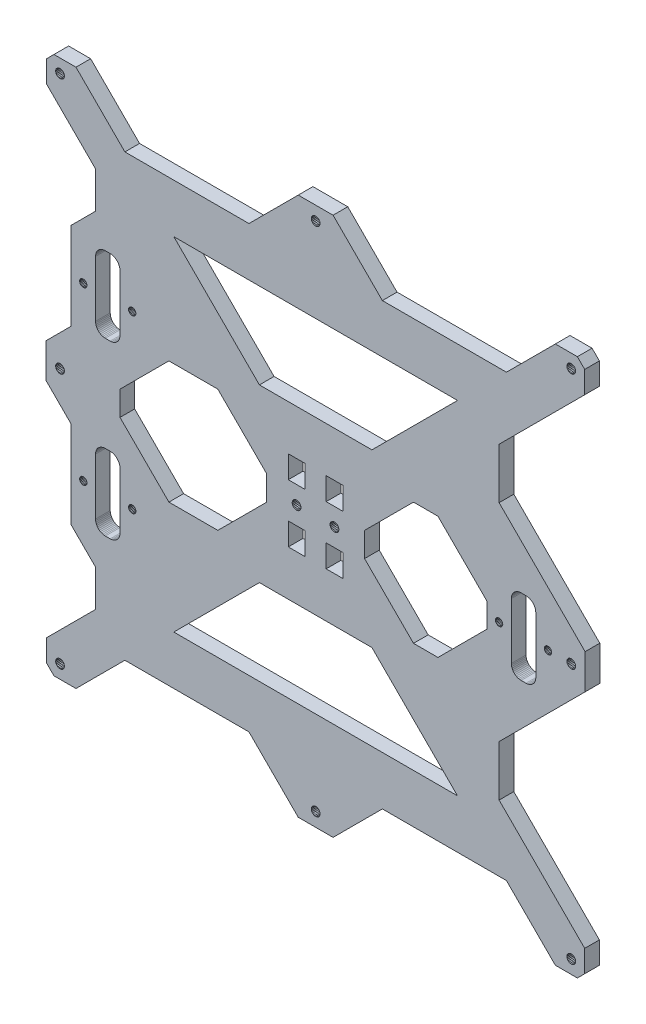
SolidWorks part; units mm, degrees
material "Maple"
ref_plane "Front Plane" through (0, 0, 0) normal (0, 0, 1) x (1, 0, 0)
ref_plane "Top Plane" through (0, 0, 0) normal (0, 1, 0) x (1, 0, 0)
ref_plane "Right Plane" through (0, 0, 0) normal (1, 0, 0) x (0, 0, -1)
sketch "Sketch1" plane through (0, 0, 0) normal (0, 0, 1) x (1, 0, 0)
  line L6332 (263.5741, 229.7904) -> (263.1048, 229.5589)
  line L6333 (262.6698, 229.2683) -> (262.2764, 228.9233)
  line L6334 (263.1048, 229.5589) -> (262.6698, 229.2683)
  line L6335 (253.1049, 139.0949) -> (273.1048, 159.0949)
  line L6336 (251.1049, 196.0949) -> (261.1048, 186.0949)
  line L6337 (261.1048, 312.0948) -> (251.1049, 302.0948)
  line L6338 (241.1049, 151.0949) -> (241.1049, 142.0949)
  line L6339 (274.8058, 284.8448) -> (274.656, 284.4831)
  line L6340 (269.9333, 200.2664) -> (270.2783, 200.6598)
  line L6341 (268.6356, 229.7904) -> (268.1401, 229.9585)
  line L6342 (268.1401, 229.9585) -> (267.627, 230.0606)
  line L6343 (267.627, 230.0606) -> (267.1048, 230.0948)
  line L6344 (241.1049, 142.0949) -> (244.1049, 139.0949)
  line L6345 (271.0706, 202.5727) -> (271.1048, 203.0948)
  line L6346 (267.627, 199.1291) -> (268.1401, 199.2311)
  line L6347 (263.5741, 199.3993) -> (264.0696, 199.2311)
  line L6348 (263.1048, 199.6307) -> (263.5741, 199.3993)
  line L6349 (461.1048, 347.0948) -> (426.1048, 312.0948)
  line L6350 (269.1048, 229.5589) -> (268.6356, 229.7904)
  line L6351 (261.4093, 227.6256) -> (261.2411, 227.1301)
  line L6352 (261.2411, 227.1301) -> (261.1391, 226.6169)
  line L6353 (261.1391, 226.6169) -> (261.1048, 226.0948)
  line L6354 (265.1048, 230.0948) -> (267.1048, 230.0948)
  line L6355 (449.1048, 139.0949) -> (429.1048, 159.0949)
  line L6356 (253.1049, 359.0948) -> (273.1048, 339.0948)
  line L6357 (262.6698, 199.9214) -> (263.1048, 199.6307)
  line L6358 (262.2764, 200.2664) -> (262.6698, 199.9214)
  line L6359 (267.1048, 199.0949) -> (265.1048, 199.0949)
  line L6360 (265.1048, 230.0948) -> (264.5827, 230.0606)
  line L6361 (264.5827, 230.0606) -> (264.0696, 229.9585)
  line L6362 (261.1048, 203.0948) -> (261.1048, 226.0948)
  line L6363 (261.1048, 203.0948) -> (261.1391, 202.5727)
  line L6364 (261.1391, 202.5727) -> (261.2411, 202.0596)
  line L6365 (241.1049, 347.0948) -> (261.1048, 327.0948)
  line L6366 (270.9686, 227.1301) -> (270.8004, 227.6256)
  line L6367 (271.0706, 226.6169) -> (270.9686, 227.1301)
  line L6368 (271.1048, 226.0948) -> (271.0706, 226.6169)
  line L6369 (244.1049, 359.0948) -> (241.1049, 356.0948)
  line L6370 (458.1048, 359.0948) -> (449.1048, 359.0948)
  line L6371 (251.1049, 231.7916) -> (251.1049, 196.0949)
  line L6372 (270.8004, 227.6256) -> (270.5689, 228.0948)
  line L6373 (270.5689, 228.0948) -> (270.2783, 228.5299)
  line L6374 (461.1048, 151.0949) -> (461.1048, 142.0949)
  line L6375 (261.1048, 171.0949) -> (261.1048, 186.0949)
  line L6376 (261.4093, 201.5641) -> (261.6407, 201.0949)
  line L6377 (261.6407, 201.0949) -> (261.9314, 200.6598)
  line L6378 (270.2783, 228.5299) -> (269.9333, 228.9233)
  line L6379 (261.9314, 200.6598) -> (262.2764, 200.2664)
  line L6380 (271.1048, 226.0948) -> (271.1048, 203.0948)
  line L6381 (261.6407, 228.0948) -> (261.4093, 227.6256)
  line L6382 (268.6356, 199.3993) -> (269.1048, 199.6307)
  line L6383 (269.1048, 199.6307) -> (269.5399, 199.9214)
  line L6384 (269.5399, 199.9214) -> (269.9333, 200.2664)
  line L6385 (268.1401, 199.2311) -> (268.6356, 199.3993)
  line L6386 (458.1048, 139.0949) -> (461.1048, 142.0949)
  line L6387 (270.8004, 201.5641) -> (270.9686, 202.0596)
  line L6388 (270.9686, 202.0596) -> (271.0706, 202.5727)
  line L6389 (269.5399, 229.2683) -> (269.1048, 229.5589)
  line L6390 (269.9333, 228.9233) -> (269.5399, 229.2683)
  line L6391 (449.1048, 359.0948) -> (429.1048, 339.0948)
  line L6392 (241.1049, 151.0949) -> (261.1048, 171.0949)
  line L6393 (261.1048, 327.0948) -> (261.1048, 312.0948)
  line L6394 (264.0696, 229.9585) -> (263.5741, 229.7904)
  line L6395 (461.1048, 356.0948) -> (458.1048, 359.0948)
  line L6396 (251.1049, 302.0948) -> (251.1049, 266.3687)
  line L6397 (267.1048, 199.0949) -> (267.627, 199.1291)
  line L6398 (264.0696, 199.2311) -> (264.5827, 199.1291)
  line L6399 (261.9314, 228.5299) -> (261.6407, 228.0948)
  line L6400 (262.2764, 228.9233) -> (261.9314, 228.5299)
  line L6401 (270.2783, 200.6598) -> (270.5689, 201.0949)
  line L6402 (270.5689, 201.0949) -> (270.8004, 201.5641)
  line L6403 (261.2411, 202.0596) -> (261.4093, 201.5641)
  line L6404 (264.5827, 199.1291) -> (265.1048, 199.0949)
  line L6405 (445.0441, 248.0342) -> (445.3548, 247.7958)
  line L6406 (427.4038, 249.8448) -> (427.1655, 250.1555)
  line L6407 (358.2261, 359.2474) -> (343.9835, 359.2474)
  line L6408 (343.9835, 138.9423) -> (358.2261, 138.9423)
  line L6409 (240.9376, 256.2015) -> (240.9376, 241.9588)
  line L6410 (273.1048, 339.0948) -> (323.831, 339.0948)
  line L6411 (378.3787, 339.0948) -> (429.1048, 339.0948)
  line L6412 (426.1048, 186.0949) -> (426.1048, 206.821)
  line L6413 (273.1048, 159.0949) -> (323.831, 159.0949)
  line L6414 (378.3787, 159.0949) -> (429.1048, 159.0949)
  line L6415 (461.272, 241.9882) -> (461.272, 256.2308)
  line L6416 (426.1048, 291.3981) -> (426.1048, 312.0948)
  line L6417 (433.5741, 263.6532) -> (433.1048, 263.4218)
  line L6418 (270.9686, 297.1371) -> (270.8004, 297.6326)
  line L6419 (270.8004, 297.6326) -> (270.5689, 298.1019)
  line L6420 (433.1048, 263.4218) -> (432.6697, 263.1311)
  line L6421 (270.2783, 298.5369) -> (269.9333, 298.9303)
  line L6422 (275.0442, 285.1555) -> (274.8058, 284.8448)
  line L6423 (275.3548, 285.3939) -> (275.0442, 285.1555)
  line L6424 (275.7166, 285.5437) -> (275.3548, 285.3939)
  line L6425 (276.1048, 285.5948) -> (275.7166, 285.5437)
  line L6426 (276.4931, 285.5437) -> (276.1048, 285.5948)
  line L6427 (276.8548, 285.3939) -> (276.4931, 285.5437)
  line L6428 (277.1655, 285.1555) -> (276.8548, 285.3939)
  line L6429 (277.4039, 284.8448) -> (277.1655, 285.1555)
  line L6430 (277.5537, 284.4831) -> (277.4039, 284.8448)
  line L6431 (277.6048, 284.0948) -> (277.5537, 284.4831)
  line L6432 (277.5537, 283.7066) -> (277.6048, 284.0948)
  line L6433 (277.4039, 283.3448) -> (277.5537, 283.7066)
  line L6434 (277.1655, 283.0342) -> (277.4039, 283.3448)
  line L6435 (276.8548, 282.7958) -> (277.1655, 283.0342)
  line L6436 (276.4931, 282.6459) -> (276.8548, 282.7958)
  line L6437 (276.1048, 282.5948) -> (276.4931, 282.6459)
  line L6438 (275.7166, 282.6459) -> (276.1048, 282.5948)
  line L6439 (275.3548, 282.7958) -> (275.7166, 282.6459)
  line L6440 (275.0442, 283.0342) -> (275.3548, 282.7958)
  line L6441 (274.8058, 283.3448) -> (275.0442, 283.0342)
  line L6442 (274.656, 283.7066) -> (274.8058, 283.3448)
  line L6443 (274.6048, 284.0948) -> (274.656, 283.7066)
  line L6444 (274.656, 284.4831) -> (274.6048, 284.0948)
  line L6445 (444.8058, 248.3448) -> (445.0441, 248.0342)
  line L6446 (444.6559, 248.7066) -> (444.8058, 248.3448)
  line L6447 (444.6048, 249.0948) -> (444.6559, 248.7066)
  line L6448 (444.6559, 249.4831) -> (444.6048, 249.0948)
  line L6449 (444.8058, 249.8448) -> (444.6559, 249.4831)
  line L6450 (445.0441, 250.1555) -> (444.8058, 249.8448)
  line L6451 (445.3548, 250.3939) -> (445.0441, 250.1555)
  line L6452 (445.7166, 250.5437) -> (445.3548, 250.3939)
  line L6453 (446.1048, 250.5948) -> (445.7166, 250.5437)
  line L6454 (446.493, 250.5437) -> (446.1048, 250.5948)
  line L6455 (446.8548, 250.3939) -> (446.493, 250.5437)
  line L6456 (447.1655, 250.1555) -> (446.8548, 250.3939)
  line L6457 (447.4038, 249.8448) -> (447.1655, 250.1555)
  line L6458 (447.6048, 249.0948) -> (447.5537, 249.4831)
  line L6459 (447.5537, 248.7066) -> (447.6048, 249.0948)
  line L6460 (447.1655, 248.0342) -> (447.4038, 248.3448)
  line L6461 (446.8548, 247.7958) -> (447.1655, 248.0342)
  line L6462 (446.493, 247.6459) -> (446.8548, 247.7958)
  line L6463 (446.1048, 247.5948) -> (446.493, 247.6459)
  line L6464 (445.7166, 247.6459) -> (446.1048, 247.5948)
  line L6465 (445.3548, 247.7958) -> (445.7166, 247.6459)
  line L6466 (427.5537, 249.4831) -> (427.4038, 249.8448)
  line L6467 (427.6048, 249.0948) -> (427.5537, 249.4831)
  line L6468 (427.5537, 248.7066) -> (427.6048, 249.0948)
  line L6469 (427.4038, 248.3448) -> (427.5537, 248.7066)
  line L6470 (427.1655, 248.0342) -> (427.4038, 248.3448)
  line L6471 (426.8548, 247.7958) -> (427.1655, 248.0342)
  line L6472 (426.493, 247.6459) -> (426.8548, 247.7958)
  line L6473 (426.1048, 247.5948) -> (426.493, 247.6459)
  line L6474 (425.7166, 247.6459) -> (426.1048, 247.5948)
  line L6475 (425.3548, 247.7958) -> (425.7166, 247.6459)
  line L6476 (425.0441, 248.0342) -> (425.3548, 247.7958)
  line L6477 (424.8058, 248.3448) -> (425.0441, 248.0342)
  line L6478 (424.6559, 248.7066) -> (424.8058, 248.3448)
  line L6479 (424.6048, 249.0948) -> (424.6559, 248.7066)
  line L6480 (424.6559, 249.4831) -> (424.6048, 249.0948)
  line L6481 (424.8058, 249.8448) -> (424.6559, 249.4831)
  line L6482 (425.0441, 250.1555) -> (424.8058, 249.8448)
  line L6483 (425.3548, 250.3939) -> (425.0441, 250.1555)
  line L6484 (425.7166, 250.5437) -> (425.3548, 250.3939)
  line L6485 (426.1048, 250.5948) -> (425.7166, 250.5437)
  line L6486 (426.493, 250.5437) -> (426.1048, 250.5948)
  line L6487 (426.8548, 250.3939) -> (426.493, 250.5437)
  line L6488 (427.1655, 250.1555) -> (426.8548, 250.3939)
  line L6489 (434.0695, 263.8214) -> (433.5741, 263.6532)
  line L6490 (434.5827, 263.9235) -> (434.0695, 263.8214)
  line L6491 (435.1048, 263.9577) -> (434.5827, 263.9235)
  line L6492 (435.1048, 263.9577) -> (437.1048, 263.9577)
  line L6493 (437.6269, 263.9235) -> (437.1048, 263.9577)
  line L6494 (438.1401, 263.8214) -> (437.6269, 263.9235)
  line L6495 (438.6355, 263.6532) -> (438.1401, 263.8214)
  line L6496 (439.1048, 263.4218) -> (438.6355, 263.6532)
  line L6497 (439.5398, 263.1311) -> (439.1048, 263.4218)
  line L6498 (439.9332, 262.7861) -> (439.5398, 263.1311)
  line L6499 (440.2782, 262.3928) -> (439.9332, 262.7861)
  line L6500 (440.5689, 261.9577) -> (440.2782, 262.3928)
  line L6501 (440.8003, 261.4884) -> (440.5689, 261.9577)
  line L6502 (440.9685, 260.993) -> (440.8003, 261.4884)
  line L6503 (441.0706, 260.4798) -> (440.9685, 260.993)
  line L6504 (441.1048, 259.9577) -> (441.0706, 260.4798)
  line L6505 (441.1048, 259.9577) -> (441.1048, 236.9577)
  line L6506 (441.0706, 236.4356) -> (441.1048, 236.9577)
  line L6507 (440.9685, 235.9224) -> (441.0706, 236.4356)
  line L6508 (440.8003, 235.427) -> (440.9685, 235.9224)
  line L6509 (440.5689, 234.9577) -> (440.8003, 235.427)
  line L6510 (440.2782, 234.5227) -> (440.5689, 234.9577)
  line L6511 (439.9332, 234.1293) -> (440.2782, 234.5227)
  line L6512 (439.5398, 233.7843) -> (439.9332, 234.1293)
  line L6513 (439.1048, 233.4936) -> (439.5398, 233.7843)
  line L6514 (438.6355, 233.2622) -> (439.1048, 233.4936)
  line L6515 (438.1401, 233.094) -> (438.6355, 233.2622)
  line L6516 (437.6269, 232.9919) -> (438.1401, 233.094)
  line L6517 (437.1048, 232.9577) -> (437.6269, 232.9919)
  line L6518 (437.1048, 232.9577) -> (435.1048, 232.9577)
  line L6519 (434.5827, 232.9919) -> (435.1048, 232.9577)
  line L6520 (434.0695, 233.094) -> (434.5827, 232.9919)
  line L6521 (433.5741, 233.2622) -> (434.0695, 233.094)
  line L6522 (433.1048, 233.4936) -> (433.5741, 233.2622)
  line L6523 (432.6697, 233.7843) -> (433.1048, 233.4936)
  line L6524 (432.2764, 234.1293) -> (432.6697, 233.7843)
  line L6525 (431.9314, 234.5227) -> (432.2764, 234.1293)
  line L6526 (431.6407, 234.9577) -> (431.9314, 234.5227)
  line L6527 (431.4093, 235.427) -> (431.6407, 234.9577)
  line L6528 (431.2411, 235.9224) -> (431.4093, 235.427)
  line L6529 (431.139, 236.4356) -> (431.2411, 235.9224)
  line L6530 (431.1048, 236.9577) -> (431.139, 236.4356)
  line L6531 (431.1048, 236.9577) -> (431.1048, 259.9577)
  line L6532 (431.139, 260.4798) -> (431.1048, 259.9577)
  line L6533 (431.2411, 260.993) -> (431.139, 260.4798)
  line L6534 (431.4093, 261.4884) -> (431.2411, 260.993)
  line L6535 (431.6407, 261.9577) -> (431.4093, 261.4884)
  line L6536 (431.9314, 262.3928) -> (431.6407, 261.9577)
  line L6537 (432.2764, 262.7861) -> (431.9314, 262.3928)
  line L6538 (432.6697, 263.1311) -> (432.2764, 262.7861)
  line L6539 (271.0706, 296.624) -> (270.9686, 297.1371)
  line L6540 (271.1048, 296.1019) -> (271.0706, 296.624)
  line L6541 (271.1048, 296.1019) -> (271.1048, 273.1019)
  line L6542 (271.0706, 272.5798) -> (271.1048, 273.1019)
  line L6543 (270.9686, 272.0666) -> (271.0706, 272.5798)
  line L6544 (270.8004, 271.5711) -> (270.9686, 272.0666)
  line L6545 (270.5689, 271.1019) -> (270.8004, 271.5711)
  line L6546 (270.2783, 270.6668) -> (270.5689, 271.1019)
  line L6547 (269.9333, 270.2734) -> (270.2783, 270.6668)
  line L6548 (269.5399, 269.9285) -> (269.9333, 270.2734)
  line L6549 (269.1048, 269.6378) -> (269.5399, 269.9285)
  line L6550 (268.6356, 269.4063) -> (269.1048, 269.6378)
  line L6551 (268.1401, 269.2382) -> (268.6356, 269.4063)
  line L6552 (267.627, 269.1361) -> (268.1401, 269.2382)
  line L6553 (267.1048, 269.1019) -> (267.627, 269.1361)
  line L6554 (267.1048, 269.1019) -> (265.1048, 269.1019)
  line L6555 (264.5827, 269.1361) -> (265.1048, 269.1019)
  line L6556 (264.0696, 269.2382) -> (264.5827, 269.1361)
  line L6557 (263.5741, 269.4063) -> (264.0696, 269.2382)
  line L6558 (263.1048, 269.6378) -> (263.5741, 269.4063)
  line L6559 (262.6698, 269.9285) -> (263.1048, 269.6378)
  line L6560 (262.2764, 270.2734) -> (262.6698, 269.9285)
  line L6561 (261.9314, 270.6668) -> (262.2764, 270.2734)
  line L6562 (261.6407, 271.1019) -> (261.9314, 270.6668)
  line L6563 (261.4093, 271.5711) -> (261.6407, 271.1019)
  line L6564 (261.2411, 272.0666) -> (261.4093, 271.5711)
  line L6565 (261.1391, 272.5798) -> (261.2411, 272.0666)
  line L6566 (261.1048, 273.1019) -> (261.1391, 272.5798)
  line L6567 (261.1048, 273.1019) -> (261.1048, 296.1019)
  line L6568 (261.1391, 296.624) -> (261.1048, 296.1019)
  line L6569 (261.2411, 297.1371) -> (261.1391, 296.624)
  line L6570 (261.4093, 297.6326) -> (261.2411, 297.1371)
  line L6571 (261.6407, 298.1019) -> (261.4093, 297.6326)
  line L6572 (261.9314, 298.5369) -> (261.6407, 298.1019)
  line L6573 (262.2764, 298.9303) -> (261.9314, 298.5369)
  line L6574 (262.6698, 299.2753) -> (262.2764, 298.9303)
  line L6575 (263.1048, 299.566) -> (262.6698, 299.2753)
  line L6576 (263.5741, 299.7974) -> (263.1048, 299.566)
  line L6577 (264.0696, 299.9656) -> (263.5741, 299.7974)
  line L6578 (264.5827, 300.0676) -> (264.0696, 299.9656)
  line L6579 (265.1048, 300.1019) -> (264.5827, 300.0676)
  line L6580 (265.1048, 300.1019) -> (267.1048, 300.1019)
  line L6581 (267.627, 300.0676) -> (267.1048, 300.1019)
  line L6582 (268.1401, 299.9656) -> (267.627, 300.0676)
  line L6583 (268.6356, 299.7974) -> (268.1401, 299.9656)
  line L6584 (269.1048, 299.566) -> (268.6356, 299.7974)
  line L6585 (269.5399, 299.2753) -> (269.1048, 299.566)
  line L6586 (269.9333, 298.9303) -> (269.5399, 299.2753)
  line L6587 (270.5689, 298.1019) -> (270.2783, 298.5369)
  line L6588 (276.8548, 212.7958) -> (277.1655, 213.0342)
  line L6589 (276.4931, 212.646) -> (276.8548, 212.7958)
  line L6590 (276.1048, 212.5948) -> (276.4931, 212.646)
  line L6591 (275.7166, 212.646) -> (276.1048, 212.5948)
  line L6592 (275.3548, 212.7958) -> (275.7166, 212.646)
  line L6593 (275.0442, 213.0342) -> (275.3548, 212.7958)
  line L6594 (274.8058, 213.3448) -> (275.0442, 213.0342)
  line L6595 (274.656, 213.7066) -> (274.8058, 213.3448)
  line L6596 (274.6048, 214.0948) -> (274.656, 213.7066)
  line L6597 (274.656, 214.4831) -> (274.6048, 214.0948)
  line L6598 (274.8058, 214.8448) -> (274.656, 214.4831)
  line L6599 (275.0442, 215.1555) -> (274.8058, 214.8448)
  line L6600 (275.3548, 215.3939) -> (275.0442, 215.1555)
  line L6601 (275.7166, 215.5437) -> (275.3548, 215.3939)
  line L6602 (276.1048, 215.5948) -> (275.7166, 215.5437)
  line L6603 (276.4931, 215.5437) -> (276.1048, 215.5948)
  line L6604 (276.8548, 215.3939) -> (276.4931, 215.5437)
  line L6605 (277.1655, 215.1555) -> (276.8548, 215.3939)
  line L6606 (277.4039, 214.8448) -> (277.1655, 215.1555)
  line L6607 (277.5537, 214.4831) -> (277.4039, 214.8448)
  line L6608 (277.6048, 214.0948) -> (277.5537, 214.4831)
  line L6609 (277.5537, 213.7066) -> (277.6048, 214.0948)
  line L6610 (277.4039, 213.3448) -> (277.5537, 213.7066)
  line L6611 (277.1655, 213.0342) -> (277.4039, 213.3448)
  line L6612 (352.6637, 352.7052) -> (352.8435, 353.1393)
  line L6613 (352.3776, 352.3324) -> (352.6637, 352.7052)
  line L6614 (352.0048, 352.0463) -> (352.3776, 352.3324)
  line L6615 (351.5707, 351.8665) -> (352.0048, 352.0463)
  line L6616 (351.1048, 351.8052) -> (351.5707, 351.8665)
  line L6617 (350.6389, 351.8665) -> (351.1048, 351.8052)
  line L6618 (350.2048, 352.0463) -> (350.6389, 351.8665)
  line L6619 (349.832, 352.3324) -> (350.2048, 352.0463)
  line L6620 (349.546, 352.7052) -> (349.832, 352.3324)
  line L6621 (349.3662, 353.1393) -> (349.546, 352.7052)
  line L6622 (349.3048, 353.6052) -> (349.3662, 353.1393)
  line L6623 (349.3662, 354.0711) -> (349.3048, 353.6052)
  line L6624 (349.546, 354.5052) -> (349.3662, 354.0711)
  line L6625 (349.832, 354.878) -> (349.546, 354.5052)
  line L6626 (350.2048, 355.164) -> (349.832, 354.878)
  line L6627 (351.1048, 355.4052) -> (350.6389, 355.3438)
  line L6628 (351.5707, 355.3438) -> (351.1048, 355.4052)
  line L6629 (352.0048, 355.164) -> (351.5707, 355.3438)
  line L6630 (352.0385, 355.1317) -> (352.0048, 355.164)
  line L6631 (352.3776, 354.878) -> (352.0385, 355.1317)
  line L6632 (352.6637, 354.5052) -> (352.3776, 354.878)
  line L6633 (352.8435, 354.0711) -> (352.6637, 354.5052)
  line L6634 (352.9048, 353.6052) -> (352.8435, 354.0711)
  line L6635 (352.8435, 353.1393) -> (352.9048, 353.6052)
  line L6636 (256.1049, 285.5948) -> (255.7166, 285.5437)
  line L6637 (256.4931, 285.5437) -> (256.1049, 285.5948)
  line L6638 (256.8549, 285.3939) -> (256.4931, 285.5437)
  line L6639 (257.1655, 285.1555) -> (256.8549, 285.3939)
  line L6640 (257.4039, 284.8448) -> (257.1655, 285.1555)
  line L6641 (257.5537, 284.4831) -> (257.4039, 284.8448)
  line L6642 (257.6049, 284.0948) -> (257.5537, 284.4831)
  line L6643 (257.5537, 283.7066) -> (257.6049, 284.0948)
  line L6644 (257.4039, 283.3448) -> (257.5537, 283.7066)
  line L6645 (257.1655, 283.0342) -> (257.4039, 283.3448)
  line L6646 (256.8549, 282.7958) -> (257.1655, 283.0342)
  line L6647 (256.4931, 282.6459) -> (256.8549, 282.7958)
  line L6648 (256.1049, 282.5948) -> (256.4931, 282.6459)
  line L6649 (255.7166, 282.6459) -> (256.1049, 282.5948)
  line L6650 (255.3549, 282.7958) -> (255.7166, 282.6459)
  line L6651 (255.0442, 283.0342) -> (255.3549, 282.7958)
  line L6652 (254.8058, 283.3448) -> (255.0442, 283.0342)
  line L6653 (254.656, 283.7066) -> (254.8058, 283.3448)
  line L6654 (254.6049, 284.0948) -> (254.656, 283.7066)
  line L6655 (254.656, 284.4831) -> (254.6049, 284.0948)
  line L6656 (254.8058, 284.8448) -> (254.656, 284.4831)
  line L6657 (255.0442, 285.1555) -> (254.8058, 284.8448)
  line L6658 (255.3549, 285.3939) -> (255.0442, 285.1555)
  line L6659 (255.7166, 285.5437) -> (255.3549, 285.3939)
  line L6660 (350.2048, 146.1433) -> (349.832, 145.8573)
  line L6661 (350.6389, 146.3232) -> (350.2048, 146.1433)
  line L6662 (351.1048, 146.3845) -> (350.6389, 146.3232)
  line L6663 (351.5707, 146.3232) -> (351.1048, 146.3845)
  line L6664 (352.0048, 146.1433) -> (351.5707, 146.3232)
  line L6665 (352.3776, 145.8573) -> (352.0048, 146.1433)
  line L6666 (352.6637, 145.4845) -> (352.3776, 145.8573)
  line L6667 (352.8435, 145.0504) -> (352.6637, 145.4845)
  line L6668 (352.9048, 144.5845) -> (352.8435, 145.0504)
  line L6669 (352.8435, 144.1186) -> (352.9048, 144.5845)
  line L6670 (352.6637, 143.6845) -> (352.8435, 144.1186)
  line L6671 (352.3776, 143.3117) -> (352.6637, 143.6845)
  line L6672 (352.0048, 143.0256) -> (352.3776, 143.3117)
  line L6673 (351.1048, 142.7845) -> (351.5707, 142.8458)
  line L6674 (350.6389, 142.8458) -> (351.1048, 142.7845)
  line L6675 (350.2048, 143.0256) -> (350.6389, 142.8458)
  line L6676 (350.1712, 143.0579) -> (350.2048, 143.0256)
  line L6677 (349.832, 143.3117) -> (350.1712, 143.0579)
  line L6678 (349.546, 143.6845) -> (349.832, 143.3117)
  line L6679 (349.3662, 144.1186) -> (349.546, 143.6845)
  line L6680 (349.3048, 144.5845) -> (349.3662, 144.1186)
  line L6681 (349.3662, 145.0504) -> (349.3048, 144.5845)
  line L6682 (349.546, 145.4845) -> (349.3662, 145.0504)
  line L6683 (349.832, 145.8573) -> (349.546, 145.4845)
  line L6684 (293.1048, 319.0948) -> (409.1048, 319.0948)
  line L6685 (409.1048, 319.0948) -> (374.1048, 284.0948)
  line L6686 (374.1048, 284.0948) -> (328.1048, 284.0948)
  line L6687 (293.1048, 319.0948) -> (328.1048, 284.0948)
  line L6688 (456.5152, 146.1433) -> (456.081, 146.3232)
  line L6689 (456.888, 145.8573) -> (456.5152, 146.1433)
  line L6690 (457.174, 145.4845) -> (456.888, 145.8573)
  line L6691 (457.3538, 145.0504) -> (457.174, 145.4845)
  line L6692 (457.4152, 144.5845) -> (457.3538, 145.0504)
  line L6693 (457.3538, 144.1186) -> (457.4152, 144.5845)
  line L6694 (457.174, 143.6845) -> (457.3538, 144.1186)
  line L6695 (456.888, 143.3117) -> (457.174, 143.6845)
  line L6696 (456.5152, 143.0256) -> (456.888, 143.3117)
  line L6697 (456.081, 142.8458) -> (456.5152, 143.0256)
  line L6698 (455.6152, 142.7845) -> (456.081, 142.8458)
  line L6699 (455.1493, 142.8458) -> (455.6152, 142.7845)
  line L6700 (454.7152, 143.0256) -> (455.1493, 142.8458)
  line L6701 (454.3424, 143.3117) -> (454.7152, 143.0256)
  line L6702 (454.0563, 143.6845) -> (454.3424, 143.3117)
  line L6703 (453.8765, 144.1186) -> (454.0563, 143.6845)
  line L6704 (453.8152, 144.5845) -> (453.8765, 144.1186)
  line L6705 (453.8765, 145.0504) -> (453.8152, 144.5845)
  line L6706 (454.0563, 145.4845) -> (453.8765, 145.0504)
  line L6707 (454.3424, 145.8573) -> (454.0563, 145.4845)
  line L6708 (454.7152, 146.1433) -> (454.3424, 145.8573)
  line L6709 (455.1493, 146.3232) -> (454.7152, 146.1433)
  line L6710 (455.6152, 146.3845) -> (455.1493, 146.3232)
  line L6711 (456.081, 146.3232) -> (455.6152, 146.3845)
  line L6712 (245.6771, 143.0566) -> (246.1092, 142.8719)
  line L6713 (245.3075, 143.3468) -> (245.6771, 143.0566)
  line L6714 (245.0257, 143.7227) -> (245.3075, 143.3468)
  line L6715 (244.8507, 144.1588) -> (245.0257, 143.7227)
  line L6716 (244.7946, 144.6254) -> (244.8507, 144.1588)
  line L6717 (244.8611, 145.0905) -> (244.7946, 144.6254)
  line L6718 (245.0458, 145.5226) -> (244.8611, 145.0905)
  line L6719 (245.336, 145.8922) -> (245.0458, 145.5226)
  line L6720 (245.712, 146.1741) -> (245.336, 145.8922)
  line L6721 (246.1481, 146.349) -> (245.712, 146.1741)
  line L6722 (246.6146, 146.4051) -> (246.1481, 146.349)
  line L6723 (247.0798, 146.3386) -> (246.6146, 146.4051)
  line L6724 (247.5118, 146.1539) -> (247.0798, 146.3386)
  line L6725 (247.8814, 145.8637) -> (247.5118, 146.1539)
  line L6726 (248.1633, 145.4878) -> (247.8814, 145.8637)
  line L6727 (248.3382, 145.0517) -> (248.1633, 145.4878)
  line L6728 (248.3944, 144.5851) -> (248.3382, 145.0517)
  line L6729 (248.3278, 144.12) -> (248.3944, 144.5851)
  line L6730 (248.1432, 143.6879) -> (248.3278, 144.12)
  line L6731 (247.853, 143.3183) -> (248.1432, 143.6879)
  line L6732 (247.477, 143.0364) -> (247.853, 143.3183)
  line L6733 (247.0409, 142.8615) -> (247.477, 143.0364)
  line L6734 (246.5743, 142.8054) -> (247.0409, 142.8615)
  line L6735 (246.1092, 142.8719) -> (246.5743, 142.8054)
  line L6736 (454.3567, 250.3818) -> (454.0665, 250.0122)
  line L6737 (454.7327, 250.6636) -> (454.3567, 250.3818)
  line L6738 (455.1688, 250.8386) -> (454.7327, 250.6636)
  line L6739 (455.6353, 250.8947) -> (455.1688, 250.8386)
  line L6740 (456.1005, 250.8282) -> (455.6353, 250.8947)
  line L6741 (456.5325, 250.6435) -> (456.1005, 250.8282)
  line L6742 (456.9021, 250.3533) -> (456.5325, 250.6435)
  line L6743 (457.184, 249.9773) -> (456.9021, 250.3533)
  line L6744 (457.3589, 249.5412) -> (457.184, 249.9773)
  line L6745 (457.4151, 249.0747) -> (457.3589, 249.5412)
  line L6746 (457.3485, 248.6095) -> (457.4151, 249.0747)
  line L6747 (457.1639, 248.1775) -> (457.3485, 248.6095)
  line L6748 (456.8736, 247.8079) -> (457.1639, 248.1775)
  line L6749 (456.4977, 247.526) -> (456.8736, 247.8079)
  line L6750 (456.0616, 247.3511) -> (456.4977, 247.526)
  line L6751 (455.595, 247.2949) -> (456.0616, 247.3511)
  line L6752 (455.1299, 247.3615) -> (455.595, 247.2949)
  line L6753 (454.6978, 247.5462) -> (455.1299, 247.3615)
  line L6754 (454.3282, 247.8364) -> (454.6978, 247.5462)
  line L6755 (454.0464, 248.2123) -> (454.3282, 247.8364)
  line L6756 (453.8714, 248.6484) -> (454.0464, 248.2123)
  line L6757 (453.8153, 249.115) -> (453.8714, 248.6484)
  line L6758 (453.8818, 249.5801) -> (453.8153, 249.115)
  line L6759 (454.0665, 250.0122) -> (453.8818, 249.5801)
  line L6760 (244.7946, 249.115) -> (244.8507, 248.6484)
  line L6761 (244.8611, 249.5801) -> (244.7946, 249.115)
  line L6762 (245.0458, 250.0122) -> (244.8611, 249.5801)
  line L6763 (245.336, 250.3818) -> (245.0458, 250.0122)
  line L6764 (245.712, 250.6636) -> (245.336, 250.3818)
  line L6765 (246.1481, 250.8386) -> (245.712, 250.6636)
  line L6766 (246.6146, 250.8947) -> (246.1481, 250.8386)
  line L6767 (247.0798, 250.8282) -> (246.6146, 250.8947)
  line L6768 (247.5118, 250.6435) -> (247.0798, 250.8282)
  line L6769 (247.8814, 250.3533) -> (247.5118, 250.6435)
  line L6770 (248.1633, 249.9773) -> (247.8814, 250.3533)
  line L6771 (248.3382, 249.5412) -> (248.1633, 249.9773)
  line L6772 (248.3944, 249.0747) -> (248.3382, 249.5412)
  line L6773 (248.3278, 248.6095) -> (248.3944, 249.0747)
  line L6774 (248.1432, 248.1775) -> (248.3278, 248.6095)
  line L6775 (247.853, 247.8079) -> (248.1432, 248.1775)
  line L6776 (247.477, 247.526) -> (247.853, 247.8079)
  line L6777 (247.0409, 247.3511) -> (247.477, 247.526)
  line L6778 (246.5743, 247.2949) -> (247.0409, 247.3511)
  line L6779 (246.1092, 247.3615) -> (246.5743, 247.2949)
  line L6780 (245.6771, 247.5462) -> (246.1092, 247.3615)
  line L6781 (245.3075, 247.8364) -> (245.6771, 247.5462)
  line L6782 (245.0257, 248.2123) -> (245.3075, 247.8364)
  line L6783 (244.8507, 248.6484) -> (245.0257, 248.2123)
  line L6784 (331.1048, 254.0948) -> (331.1048, 244.0948)
  line L6785 (331.1048, 244.0948) -> (311.1048, 224.0948)
  line L6786 (311.1048, 224.0948) -> (291.1048, 224.0948)
  line L6787 (291.1048, 224.0948) -> (271.1048, 244.0948)
  line L6788 (271.1048, 244.0948) -> (271.1048, 254.0948)
  line L6789 (271.1048, 254.0948) -> (291.1048, 274.0948)
  line L6790 (291.1048, 274.0948) -> (311.1048, 274.0948)
  line L6791 (311.1048, 274.0948) -> (331.1048, 254.0948)
  line L6792 (257.4039, 214.8448) -> (257.1655, 215.1555)
  line L6793 (257.5537, 214.4831) -> (257.4039, 214.8448)
  line L6794 (257.6049, 214.0948) -> (257.5537, 214.4831)
  line L6795 (257.5537, 213.7066) -> (257.6049, 214.0948)
  line L6796 (257.4039, 213.3448) -> (257.5537, 213.7066)
  line L6797 (257.1655, 213.0342) -> (257.4039, 213.3448)
  line L6798 (256.8549, 212.7958) -> (257.1655, 213.0342)
  line L6799 (256.4931, 212.646) -> (256.8549, 212.7958)
  line L6800 (256.1049, 212.5948) -> (256.4931, 212.646)
  line L6801 (255.7166, 212.646) -> (256.1049, 212.5948)
  line L6802 (255.3549, 212.7958) -> (255.7166, 212.646)
  line L6803 (255.0442, 213.0342) -> (255.3549, 212.7958)
  line L6804 (254.8058, 213.3448) -> (255.0442, 213.0342)
  line L6805 (254.656, 213.7066) -> (254.8058, 213.3448)
  line L6806 (254.6049, 214.0948) -> (254.656, 213.7066)
  line L6807 (254.656, 214.4831) -> (254.6049, 214.0948)
  line L6808 (254.8058, 214.8448) -> (254.656, 214.4831)
  line L6809 (255.0442, 215.1555) -> (254.8058, 214.8448)
  line L6810 (255.3549, 215.3939) -> (255.0442, 215.1555)
  line L6811 (255.7166, 215.5437) -> (255.3549, 215.3939)
  line L6812 (256.1049, 215.5948) -> (255.7166, 215.5437)
  line L6813 (256.4931, 215.5437) -> (256.1049, 215.5948)
  line L6814 (256.8549, 215.3939) -> (256.4931, 215.5437)
  line L6815 (257.1655, 215.1555) -> (256.8549, 215.3939)
  line L6816 (245.3217, 352.3324) -> (245.6945, 352.0463)
  line L6817 (245.0356, 352.7052) -> (245.3217, 352.3324)
  line L6818 (244.8558, 353.1393) -> (245.0356, 352.7052)
  line L6819 (244.7945, 353.6052) -> (244.8558, 353.1393)
  line L6820 (244.8558, 354.0711) -> (244.7945, 353.6052)
  line L6821 (245.3217, 354.878) -> (245.0356, 354.5052)
  line L6822 (245.6945, 355.164) -> (245.3217, 354.878)
  line L6823 (246.1286, 355.3438) -> (245.6945, 355.164)
  line L6824 (246.1752, 355.3448) -> (246.1286, 355.3438)
  line L6825 (246.5945, 355.4052) -> (246.1752, 355.3448)
  line L6826 (247.0603, 355.3438) -> (246.5945, 355.4052)
  line L6827 (247.4945, 355.164) -> (247.0603, 355.3438)
  line L6828 (247.8673, 354.878) -> (247.4945, 355.164)
  line L6829 (248.1533, 354.5052) -> (247.8673, 354.878)
  line L6830 (248.3331, 354.0711) -> (248.1533, 354.5052)
  line L6831 (248.3945, 353.6052) -> (248.3331, 354.0711)
  line L6832 (248.3331, 353.1393) -> (248.3945, 353.6052)
  line L6833 (248.1533, 352.7052) -> (248.3331, 353.1393)
  line L6834 (247.8673, 352.3324) -> (248.1533, 352.7052)
  line L6835 (247.4945, 352.0463) -> (247.8673, 352.3324)
  line L6836 (247.0603, 351.8665) -> (247.4945, 352.0463)
  line L6837 (246.5945, 351.8052) -> (247.0603, 351.8665)
  line L6838 (246.1286, 351.8665) -> (246.5945, 351.8052)
  line L6839 (245.6945, 352.0463) -> (246.1286, 351.8665)
  line L6840 (421.1048, 254.0948) -> (421.1048, 244.0948)
  line L6841 (401.1048, 224.0948) -> (391.1048, 224.0948)
  line L6842 (391.1048, 224.0948) -> (371.1048, 244.0948)
  line L6843 (371.1048, 244.0948) -> (371.1048, 254.0948)
  line L6844 (371.1048, 254.0948) -> (391.1048, 274.0948)
  line L6845 (391.1048, 274.0948) -> (401.1048, 274.0948)
  line L6846 (453.8765, 354.0711) -> (453.8152, 353.6052)
  line L6847 (454.0563, 354.5052) -> (453.8765, 354.0711)
  line L6848 (454.3424, 354.878) -> (454.0563, 354.5052)
  line L6849 (454.7152, 355.164) -> (454.3424, 354.878)
  line L6850 (455.1493, 355.3438) -> (454.7152, 355.164)
  line L6851 (455.6152, 355.4052) -> (455.1493, 355.3438)
  line L6852 (456.081, 355.3438) -> (455.6152, 355.4052)
  line L6853 (456.5152, 355.164) -> (456.081, 355.3438)
  line L6854 (456.888, 354.878) -> (456.5152, 355.164)
  line L6855 (457.174, 354.5052) -> (456.888, 354.878)
  line L6856 (457.3538, 354.0711) -> (457.174, 354.5052)
  line L6857 (457.4152, 353.6052) -> (457.3538, 354.0711)
  line L6858 (457.3538, 353.1393) -> (457.4152, 353.6052)
  line L6859 (457.174, 352.7052) -> (457.3538, 353.1393)
  line L6860 (456.888, 352.3324) -> (457.174, 352.7052)
  line L6861 (456.5152, 352.0463) -> (456.888, 352.3324)
  line L6862 (456.081, 351.8665) -> (456.5152, 352.0463)
  line L6863 (455.6152, 351.8052) -> (456.081, 351.8665)
  line L6864 (455.1493, 351.8665) -> (455.6152, 351.8052)
  line L6865 (454.7152, 352.0463) -> (455.1493, 351.8665)
  line L6866 (454.3424, 352.3324) -> (454.7152, 352.0463)
  line L6867 (454.0563, 352.7052) -> (454.3424, 352.3324)
  line L6868 (453.8765, 353.1393) -> (454.0563, 352.7052)
  line L6869 (453.8152, 353.6052) -> (453.8765, 353.1393)
  line L6870 (328.1048, 214.0948) -> (293.1048, 179.0949)
  line L6871 (374.1048, 214.0948) -> (328.1048, 214.0948)
  line L6872 (409.1048, 179.0949) -> (374.1048, 214.0948)
  line L6873 (293.1048, 179.0949) -> (409.1048, 179.0949)
  line L6874 (342.4015, 247.5697) -> (342.8356, 247.3899)
  line L6875 (344.2015, 247.57) -> (344.5742, 247.8561)
  line L6876 (339.903, 241.8284) -> (339.903, 232.6284)
  line L6877 (345.1012, 249.1289) -> (345.0398, 249.5948)
  line L6878 (341.5625, 249.5943) -> (341.5012, 249.1284)
  line L6879 (342.401, 250.6874) -> (342.0283, 250.4013)
  line L6880 (345.0398, 249.5948) -> (344.86, 250.0289)
  line L6881 (342.0286, 247.8557) -> (342.4015, 247.5697)
  line L6882 (344.86, 250.0289) -> (344.5739, 250.4017)
  line L6883 (343.3015, 247.3287) -> (343.7674, 247.3901)
  line L6884 (344.5742, 247.8561) -> (344.8602, 248.2289)
  line L6885 (342.0283, 250.4013) -> (341.7423, 250.0285)
  line L6886 (339.903, 265.6284) -> (339.903, 256.4284)
  line L6887 (343.7669, 250.8674) -> (343.301, 250.9287)
  line L6888 (344.8602, 248.2289) -> (345.04, 248.6631)
  line L6889 (346.703, 232.6284) -> (346.703, 241.8284)
  line L6890 (346.703, 241.8284) -> (339.903, 241.8284)
  line L6891 (341.5012, 249.1284) -> (341.5626, 248.6626)
  line L6892 (342.8351, 250.8673) -> (342.401, 250.6874)
  line L6893 (343.7674, 247.3901) -> (344.2015, 247.57)
  line L6894 (341.7425, 248.2285) -> (342.0286, 247.8557)
  line L6895 (346.703, 265.6284) -> (339.903, 265.6284)
  line L6896 (339.903, 256.4284) -> (346.703, 256.4284)
  line L6897 (344.201, 250.6877) -> (343.7669, 250.8674)
  line L6898 (344.5739, 250.4017) -> (344.201, 250.6877)
  line L6899 (341.5626, 248.6626) -> (341.7425, 248.2285)
  line L6900 (346.703, 256.4284) -> (346.703, 265.6284)
  line L6901 (345.04, 248.6631) -> (345.1012, 249.1289)
  line L6902 (339.903, 232.6284) -> (346.703, 232.6284)
  line L6903 (358.799, 247.3136) -> (359.2649, 247.375)
  line L6904 (362.2005, 232.6134) -> (362.2005, 241.8134)
  line L6905 (355.4005, 265.6133) -> (355.4005, 256.4133)
  line L6906 (357.0602, 248.6475) -> (357.2401, 248.2134)
  line L6907 (360.5375, 248.648) -> (360.5988, 249.1139)
  line L6908 (362.2005, 265.6133) -> (355.4005, 265.6133)
  line L6909 (355.4005, 232.6134) -> (362.2005, 232.6134)
  line L6910 (359.2649, 247.375) -> (359.699, 247.5549)
  line L6911 (357.2401, 248.2134) -> (357.5262, 247.8406)
  line L6912 (359.2644, 250.8523) -> (358.7985, 250.9136)
  line L6913 (357.8985, 250.6723) -> (357.5258, 250.3862)
  line L6914 (360.3575, 250.0138) -> (360.0714, 250.3866)
  line L6915 (362.2005, 256.4133) -> (362.2005, 265.6133)
  line L6916 (357.5262, 247.8406) -> (357.899, 247.5546)
  line L6917 (358.3326, 250.8522) -> (357.8985, 250.6723)
  line L6918 (362.2005, 241.8134) -> (355.4005, 241.8134)
  line L6919 (359.6985, 250.6726) -> (359.2644, 250.8523)
  line L6920 (360.0717, 247.841) -> (360.3577, 248.2138)
  line L6921 (357.5258, 250.3862) -> (357.2398, 250.0134)
  line L6922 (359.699, 247.5549) -> (360.0717, 247.841)
  line L6923 (357.899, 247.5546) -> (358.3331, 247.3749)
  line L6924 (355.4005, 256.4133) -> (362.2005, 256.4133)
  line L6925 (360.5988, 249.1139) -> (360.5374, 249.5797)
  line L6926 (356.9988, 249.1133) -> (357.0602, 248.6475)
  line L6927 (360.5374, 249.5797) -> (360.3575, 250.0138)
  line L6928 (360.0714, 250.3866) -> (359.6985, 250.6726)
  line L6929 (357.06, 249.5792) -> (356.9988, 249.1133)
  line L6930 (360.3577, 248.2138) -> (360.5375, 248.648)
  line L6931 (355.4005, 241.8134) -> (355.4005, 232.6134)
  line L8421 (241.1049, 356.0948) -> (241.1049, 347.0948)
  line L8422 (426.1048, 186.0949) -> (461.1048, 151.0949)
  line L8423 (461.1048, 356.0948) -> (461.1048, 347.0948)
  line L8424 (253.1049, 359.0948) -> (244.1049, 359.0948)
  line L8425 (458.1048, 139.0949) -> (449.1048, 139.0949)
  line L8426 (244.1049, 139.0949) -> (253.1049, 139.0949)
  line L8427 (323.831, 339.0948) -> (343.9835, 359.2474)
  line L8428 (378.3787, 339.0948) -> (358.2261, 359.2474)
  line L8429 (343.9835, 138.9423) -> (323.831, 159.0949)
  line L8430 (378.3787, 159.0949) -> (358.2261, 138.9423)
  line L8431 (240.9376, 241.9588) -> (251.1049, 231.7916)
  line L8432 (240.9376, 256.2015) -> (251.1049, 266.3687)
  line L8433 (461.272, 256.2308) -> (426.1048, 291.3981)
  line L8434 (461.272, 241.9882) -> (426.1048, 206.821)
  line L8435 (447.4038, 249.8448) -> (447.5537, 249.4831)
  line L8436 (447.5537, 248.7066) -> (447.4038, 248.3448)
  line L8437 (350.2048, 355.164) -> (350.6389, 355.3438)
  line L8438 (352.0048, 143.0256) -> (351.5707, 142.8458)
  line L8439 (244.8558, 354.0711) -> (245.0356, 354.5052)
  line L8440 (421.1048, 244.0948) -> (401.1048, 224.0948)
  line L8441 (401.1048, 274.0948) -> (421.1048, 254.0948)
  line L8442 (342.8356, 247.3899) -> (343.3015, 247.3287)
  line L8443 (343.301, 250.9287) -> (342.8351, 250.8673)
  line L8444 (341.7423, 250.0285) -> (341.5625, 249.5943)
  line L8445 (358.7985, 250.9136) -> (358.3326, 250.8522)
  line L8446 (358.3331, 247.3749) -> (358.799, 247.3136)
  line L8447 (357.2398, 250.0134) -> (357.06, 249.5792)
  line L9423 (411.1752, 234.1652) -> (411.1752, 234.0948)
  line L9424 (311.1048, 274.0948) -> (311.1752, 274.0948)
  line L9425 (411.1752, 264.0948) -> (411.1752, 264.0245)
  line L9426 (349.8841, 247.3437) -> (349.8841, 251.6516)
  line L9427 (349.8841, 251.6516) -> (351.3701, 247.3437)
  line L9428 (351.3701, 247.3437) -> (352.8499, 251.6516)
  line L9429 (352.8499, 251.6516) -> (352.8499, 247.3437)
  line L9430 (352.8499, 247.3437) -> (352.8499, 251.6516)
  line L9431 (352.8499, 251.6516) -> (351.3701, 247.3437)
  line L9432 (351.3701, 247.3437) -> (349.8841, 251.6516)
  line L9433 (349.8841, 251.6516) -> (349.8841, 247.3437)
extrude "Boss-Extrude1" add sketch "Sketch1" along normal blind 6
